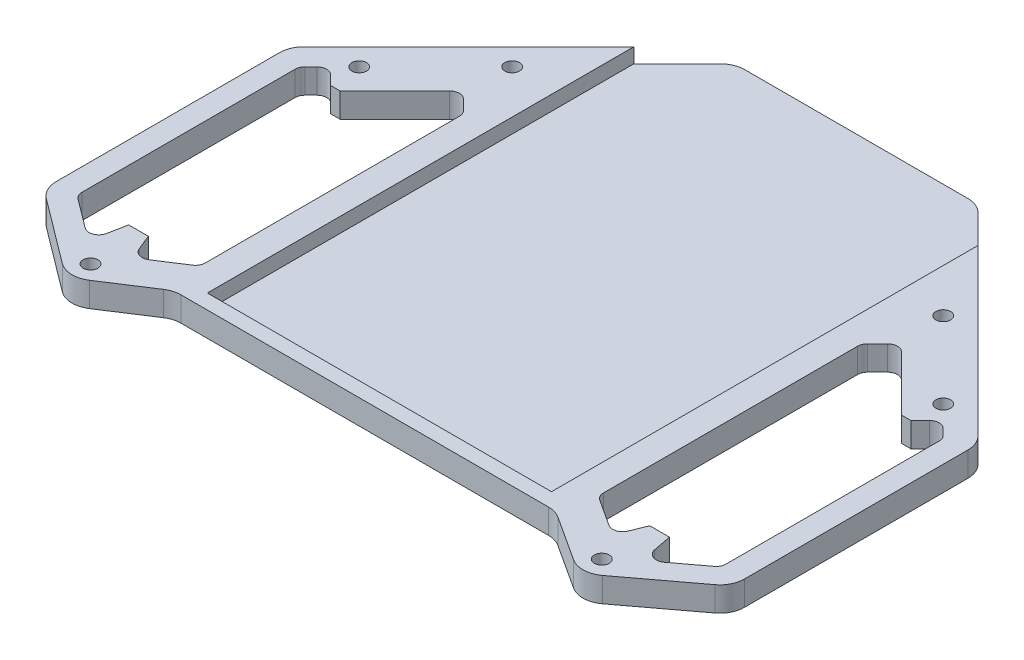
SolidWorks part; units mm, degrees
ref_plane "Front Plane" through (0, 0, 0) normal (0, 0, 1) x (1, 0, 0)
ref_plane "Top Plane" through (0, 0, 0) normal (0, 1, 0) x (1, 0, 0)
ref_plane "Right Plane" through (0, 0, 0) normal (1, 0, 0) x (0, 0, -1)
sketch "Sketch1" plane through (0, 0, 0) normal (0, 1, 0) x (1, 0, 0)
  line L0 (-52.1641, -38.6452) -> (-70, -25.2479)
  line L1 (-70, -25.2479) -> (-70, 24.7523)
  line L2 (-70, 24.7523) -> (-24.7523, 70)
  line L3 (-52.1641, -38.6452) -> (-38.8516, -30)
  line L4 (0, -30) -> (0, 70)
  line L5 (0, -30) -> (-38.8516, -30)
  line L6 (-59.397, 28.2843) -> (-43.8406, 43.8406) construction
  line L7 (-51.9976, -33.7676) -> (-63.9796, -15.3169) construction
  line L8 (-24.7523, 70) -> (0, 70)
  line L9 (0, 0) -> (-85, 0) construction
  line L10 (-43.8406, 43.8406) -> (0, 0) construction
  line L11 (-51.9976, -33.7676) -> (0, 0) construction
  line L12 (-59.0038, 22.1) -> (-57.096, 22.1)
  line L13 (-65.5, 22.1812) -> (-65.5, -23)
  line L14 (-55, -23) -> (-51, -23)
  line L15 (-40.5, 30.6005) -> (-40.5, -23)
  line L16 (-53, 22.1) -> (-53, -23) construction
  line L17 (-65.5, 22.1812) -> (-62.2925, 25.3887)
  line L18 (-62.2925, 25.3887) -> (-59.0038, 22.1)
  line L19 (-57.096, 22.1) -> (-44.5477, 34.6482)
  line L20 (-44.5477, 34.6482) -> (-40.5, 30.6005)
  line L21 (-65.5, -23) -> (-56.3366, -29.883)
  line L22 (-56.3366, -29.883) -> (-55, -23)
  line L23 (-51, -23) -> (-48.7962, -28.3876)
  line L24 (-48.7962, -28.3876) -> (-40.5, -23)
  circle A0 centre (0, 0) radius 85 construction
  circle A1 centre (-43.8406, 43.8406) radius 1.5
  circle A2 centre (-51.9976, -33.7676) radius 1.5
  circle A3 centre (-59.397, 28.2843) radius 1.5
  circle A4 centre (-63.9796, -15.3169) radius 1.5 construction
  dimension "D7" = 3
  dimension "D17" = 170
  dimension "D20" = 12.5
  dimension "D2" = 30
  dimension "D3" = 4
  dimension "D4" = 4
  dimension "D5" = 4.5
  dimension "D6" = 70
  dimension "D8" = 62
  dimension "D9" = 22
  dimension "D10" = 22
  dimension "D11" = 25
  dimension "D12" = 45.1
  dimension "D13" = 53
  dimension "D14" = 45
  dimension "D15" = 33
  dimension "D16" = 23
  dimension "D18" = 5
  dimension "D19" = 70
  dimension "D21" = 5
  dimension "D22" = 5
  dimension "D23" = 4
  dimension "D24" = 6
  dimension "D25" = 15
extrude "Boss-Extrude1" add sketch "Sketch1" along normal blind 5
fillet "Fillet1" radius 2 8 edges at (-40.5, 2.5, 23) (-48.7962, 2.5, 28.3876) (-56.3366, 2.5, 29.883) (-65.5, 2.5, 23) (-65.5, 2.5, -22.1812) (-62.2925, 2.5, -25.3887) (-40.5, 2.5, -30.6005) (-44.5477, 2.5, -34.6482)
mirror "Mirror1" about plane through (0, 5, 30) normal (-1, 0, 0) of "Fillet1", "Boss-Extrude1"
sketch "Sketch2" plane through (0, 5, 0) normal (0, 1, 0) x (1, 0, 0)
  line L0 (24.7523, 70) -> (-24.7523, 70) construction
  line L1 (-35, 70) -> (35, 70)
  line L2 (-35, 70) -> (-35, -27)
  line L3 (-35, -27) -> (35, -27)
  line L4 (35, 70) -> (35, -27)
  line L5 (-38.8516, -30) -> (38.8516, -30) construction
  dimension "D1" = 3
  dimension "D2" = 70
  dimension "D3" = 35
extrude "Cut-Extrude1" cut sketch "Sketch2" against normal blind 3
fillet "Fillet2" radius 5 10 edges at (70, 2.5, -24.7523) (24.7523, 1, -70) (-24.7523, 1, -70) (-70, 2.5, -24.7523) (-70, 2.5, 25.2479) (70, 2.5, 25.2479) (52.1641, 2.5, 38.6452) (38.8516, 2.5, 30) (-38.8516, 2.5, 30) (-52.1641, 2.5, 38.6452)
